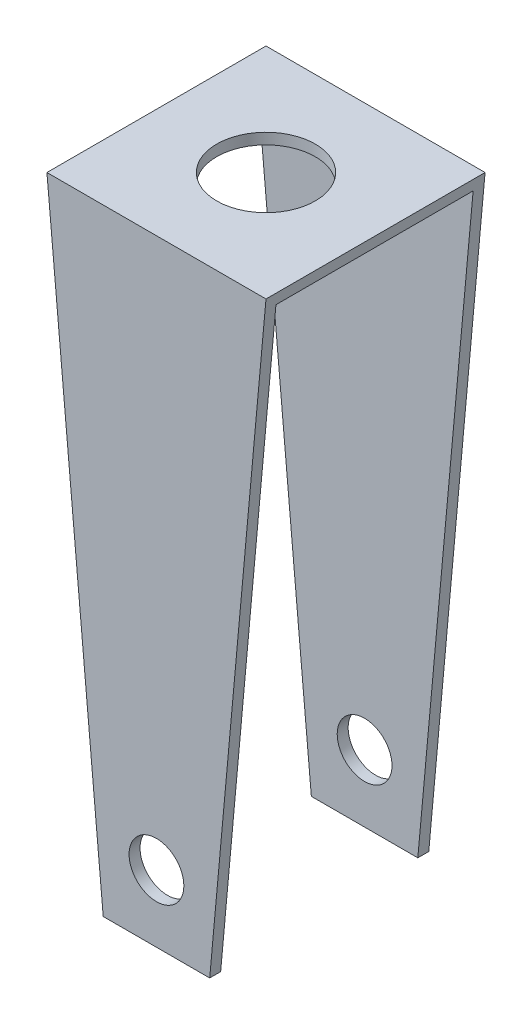
SolidWorks part; units mm, degrees
material "1060 Alloy"
ref_plane "Front Plane" through (0, 0, 0) normal (0, 0, 1) x (1, 0, 0)
ref_plane "Top Plane" through (0, 0, 0) normal (0, 1, 0) x (1, 0, 0)
ref_plane "Right Plane" through (0, 0, 0) normal (1, 0, 0) x (0, 0, -1)
sketch "Sketch1" plane through (0, 0, 0) normal (1, 0, 0) x (0, 0, -1)
  line L0 (-0.9, -2.5976) -> (-1, -2.5976)
  line L2 (-0.9, -2.5976) -> (-0.9, 2.9279)
  line L3 (-0.9, 2.9279) -> (0.9, 2.9279)
  line L4 (0.9, -2.5976) -> (0.9, 2.9279)
  line L5 (0, 3.0279) -> (0, -2.5417) construction
  line L8 (-1, -2.5976) -> (-1, 3.0279)
  line L9 (-1, 3.0279) -> (1, 3.0279)
  line L10 (1, -2.5976) -> (1, 3.0279)
  line L13 (0.9, -2.5976) -> (1, -2.5976)
  dimension "D1" = 2
  dimension "D2" = 1.8
  dimension "D3" = 0.9
  dimension "D4" = 0.1
extrude "Boss-Extrude1" add sketch "Sketch1" along normal blind 2
sketch "Sketch2" plane through (0, 0, 1) normal (0, 0, 1) x (1, 0, 0)
  line L0 (1, 3.0279) -> (1, -1.3636) construction
  line L1 (2, 3.0279) -> (0, 3.0279) construction
  line L2 (0, 3.0279) -> (0.514, -2.5976)
  line L3 (2, -2.5976) -> (0, -2.5976) construction
  line L5 (0, 3.0279) -> (-0.4078, -2.3892)
  line L6 (-0.4078, -2.3892) -> (-0.3575, -2.9691)
  line L7 (-0.3575, -2.9691) -> (0.514, -2.5976)
  line L8 (2.4078, -2.3892) -> (2.3575, -2.9691)
  line L9 (2, 3.0279) -> (2.4078, -2.3892)
  line L10 (2, 3.0279) -> (1.486, -2.5976)
  line L11 (2.3575, -2.9691) -> (1.486, -2.5976)
extrude "Cut-Extrude1" cut sketch "Sketch2" against normal blind 2
sketch "Sketch3" plane through (0, 0, 1) normal (0, 0, 1) x (1, 0, 0)
  line L0 (1, -2.5976) -> (1, -0.5692) construction
  line L1 (1.486, -2.5976) -> (0.514, -2.5976) construction
  circle A0 centre (1, -1.987) radius 0.25
  dimension "D1" = 0.5
extrude "Cut-Extrude2" cut sketch "Sketch3" against normal blind 2
sketch "Sketch4" plane through (0, 3.0279, 0) normal (0, 1, 0) x (1, 0, 0)
  line L0 (0, 1) -> (0, -1) construction
  line L1 (2, 1) -> (0, 1) construction
  circle A0 centre (1, 0) radius 0.45
  dimension "D3" = 0.9
  dimension "D1" = 1
  dimension "D2" = 1
extrude "Cut-Extrude3" cut sketch "Sketch4" against normal blind 2
